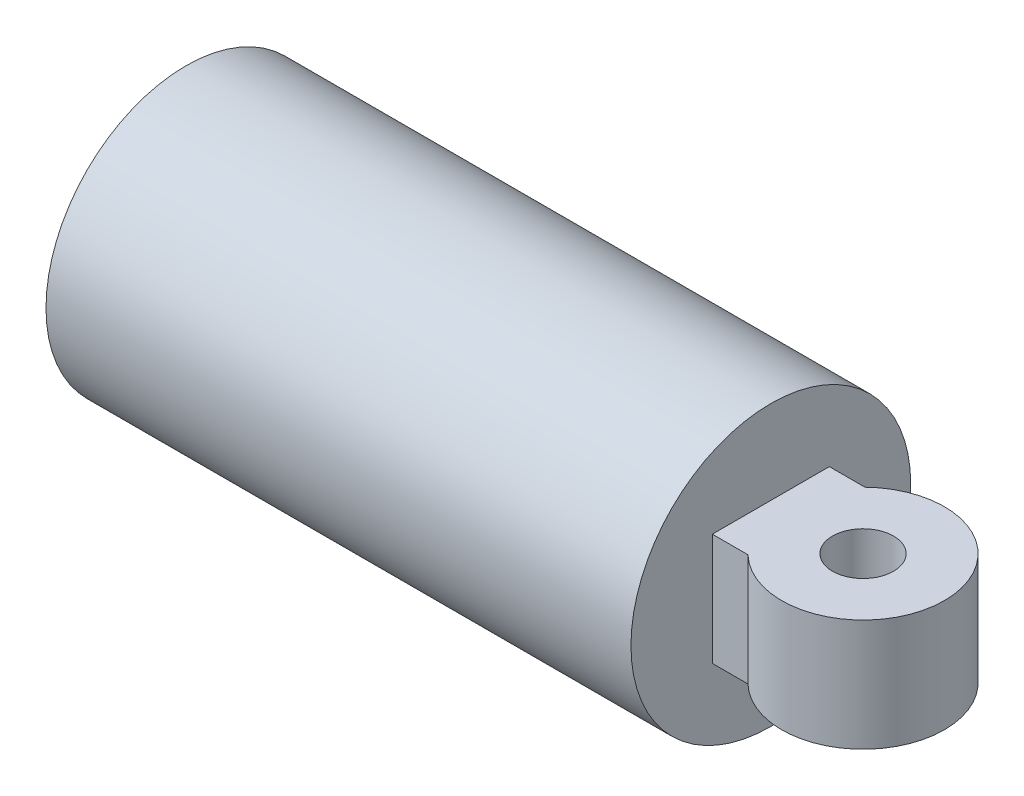
SolidWorks part; units mm, degrees
material "AISI 321 Annealed Stainless Steel (SS)"
ref_plane "Front Plane" through (0, 0, 0) normal (0, 0, 1) x (1, 0, 0)
ref_plane "Top Plane" through (0, 0, 0) normal (0, 1, 0) x (1, 0, 0)
ref_plane "Right Plane" through (0, 0, 0) normal (1, 0, 0) x (0, 0, -1)
sketch "Sketch1" plane through (0, 0, 0) normal (0, 1, 0) x (1, 0, 0)
  line L0 (0, 0) -> (-13, 0)
  line L1 (-13, 0) -> (-13, 12.5)
  line L2 (-13, 26.5) -> (-115, 26.5)
  line L3 (-115, 26.5) -> (-115, 27.5)
  line L4 (-115, 27.5) -> (0, 27.5)
  line L5 (0, 27.5) -> (0, 0)
  line L6 (-13, 12.5) -> (-113, 12.5)
  line L7 (-113, 12.5) -> (-113, 14.5)
  line L8 (-113, 14.5) -> (-13, 14.5)
  line L9 (-13, 14.5) -> (-13, 26.5)
  dimension "D1" = 1
  dimension "D2" = 115
  dimension "D3" = 13
  dimension "D4" = 27.5
  dimension "D5" = 2
  dimension "D6" = 100
  dimension "D7" = 12.5
revolve "Revolve1" add sketch "Sketch1" angle 360 about L0
sketch "Sketch2" plane through (0, 0, 0) normal (0, 1, 0) x (1, 0, 0)
  line L1 (0, 11.5) -> (7, 11.5)
  line L2 (0, 11.5) -> (0, -11.5)
  line L3 (0, -11.5) -> (7, -11.5)
  arc A0 (7, -11.5) -> (7, 11.5) centre (18.1243, 0) ccw
  circle A1 centre (18.1243, 0) radius 6
  point P7 (0, 0)
  point P9 (0, 0)
  point P10 (0, 0)
  dimension "D1" = 32
  dimension "D2" = 12
  dimension "D3" = 23
  dimension "D4" = 7
extrude "Boss-Extrude1" add sketch "Sketch2" along normal mid plane 22
